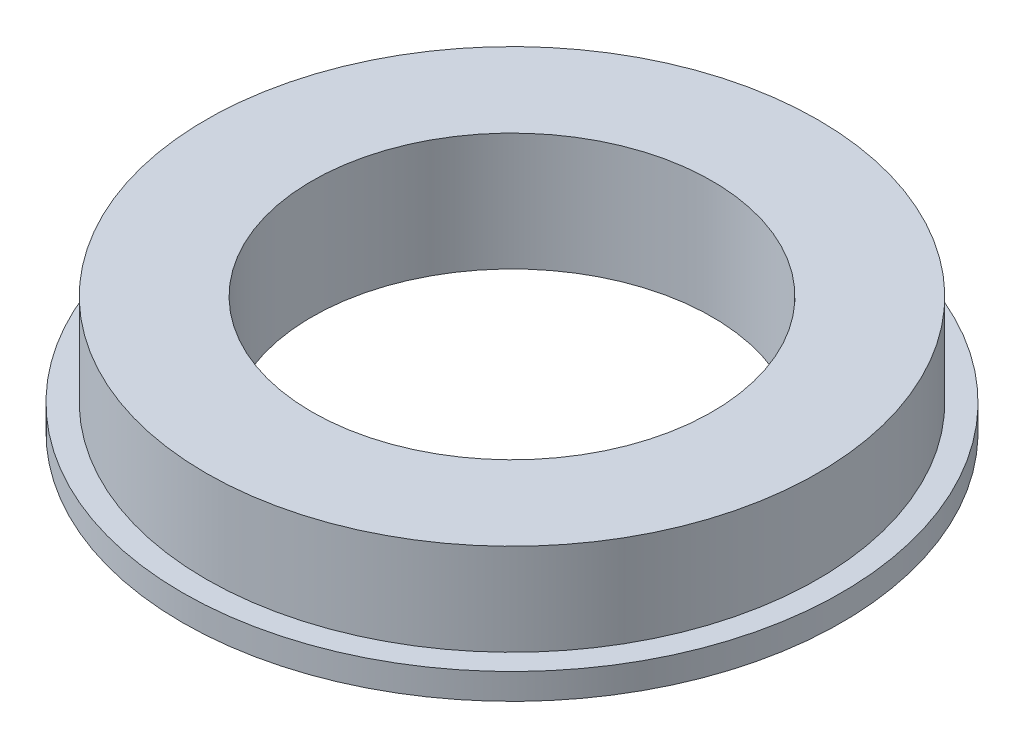
SolidWorks part; units mm, degrees
ref_plane "前视基准面" through (0, 0, 0) normal (0, 0, 1) x (1, 0, 0)
ref_plane "上视基准面" through (0, 0, 0) normal (0, 1, 0) x (1, 0, 0)
ref_plane "右视基准面" through (0, 0, 0) normal (1, 0, 0) x (0, 0, -1)
other "Configuration Table"
sketch "草图2" plane through (0, 0, 0) normal (0, 1, 0) x (1, 0, 0)
  circle A0 centre (0, 0) radius 14
  dimension "D1" = 28
extrude "凸台-拉伸1" add sketch "草图2" along normal blind 1.1
sketch "草图3" plane through (0, 1.1, 0) normal (0, 1, 0) x (1, 0, 0)
  circle A0 centre (0, 0) radius 13
  dimension "D1" = 26
extrude "凸台-拉伸2" add sketch "草图3" along normal blind 3.9
sketch "草图4" plane through (0, 5, 0) normal (0, 1, 0) x (1, 0, 0)
  circle A0 centre (0, 0) radius 8.5
  dimension "D1" = 17
extrude "切除-拉伸1" cut sketch "草图4" against normal through all
